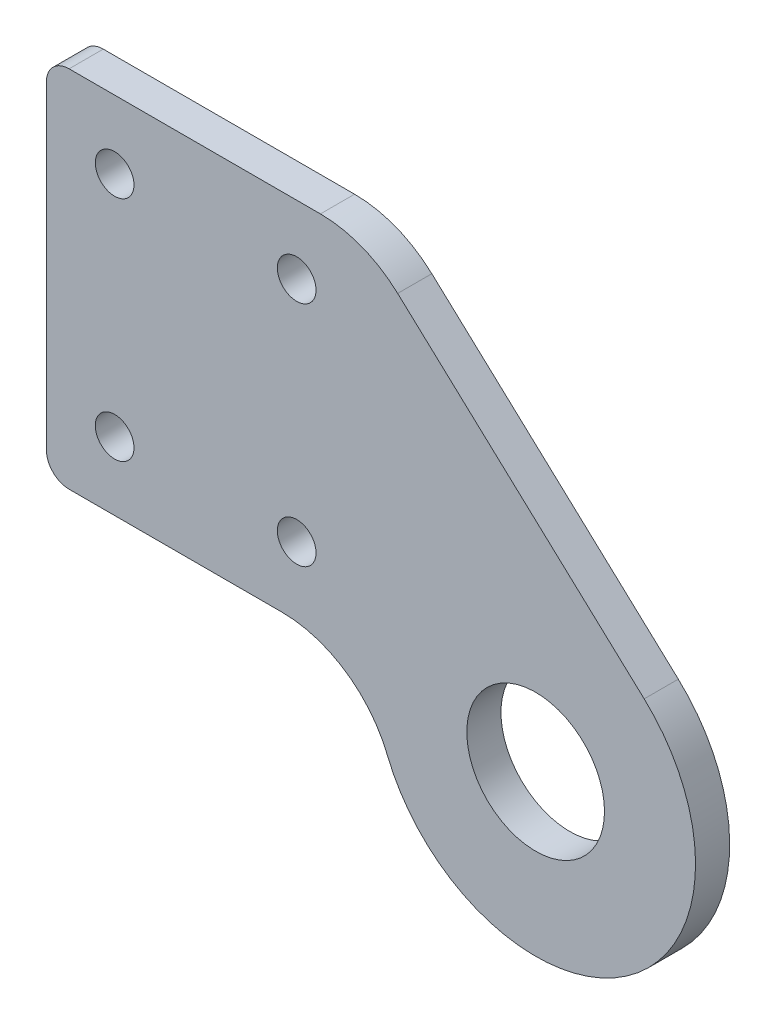
SolidWorks part; units mm, degrees
material "Hexcel AS4C (3000 Filaments)"
ref_plane "Plan de face" through (0, 0, 0) normal (0, 0, 1) x (1, 0, 0)
ref_plane "Plan de dessus" through (0, 0, 0) normal (0, 1, 0) x (1, 0, 0)
ref_plane "Plan de droite" through (0, 0, 0) normal (1, 0, 0) x (0, 0, -1)
sketch "Esquisse1" plane through (0, 0, 0) normal (0, 0, 1) x (1, 0, 0)
  line L0 (-7.5, 16.5) -> (4.7687, 5.1585)
  line L1 (-18.5, 13.5) -> (-10.5, 13.5) construction
  line L2 (-18.5, 13.5) -> (-18.5, 3.5) construction
  line L3 (-18.5, 3.5) -> (-10.5, 3.5) construction
  line L4 (-10.5, 13.5) -> (-10.5, 3.5) construction
  line L5 (-21.5, 16.5) -> (-7.5, 16.5)
  line L6 (-21.5, 16.5) -> (-21.5, 0.5)
  line L7 (-21.5, 0.5) -> (-7.5, 0.5)
  line L8 (-7.5, 16.5) -> (-7.5, 0.5) construction
  line L9 (-7.5, 0.5) -> (-7.5, 4.475) construction
  line L10 (-7.5, 4.475) -> (-5.4153, 4.475) construction
  line L11 (-7.5, 0.5) -> (-7.0072, 0.5)
  circle A0 centre (0, 0) radius 3.025
  circle A1 centre (0, 0) radius 7.025 construction
  circle A2 centre (-18.5, 13.5) radius 0.85
  circle A3 centre (-10.5, 13.5) radius 0.85
  circle A4 centre (-10.5, 3.5) radius 0.85
  circle A5 centre (-18.5, 3.5) radius 0.85
  arc A6 (-5.4153, 4.475) -> (4.7687, 5.1585) centre (0, 0) ccw construction
  arc A7 (-7.0072, 0.5) -> (4.7687, 5.1585) centre (0, 0) ccw
  dimension "D1" = 8
  dimension "D8" = 14.05
  dimension "D9" = 6.05
  dimension "D10" = 1.7
  dimension "D11" = 1.7
  dimension "D12" = 1.7
  dimension "D13" = 1.7
  dimension "D2" = 10
  dimension "D3" = 3
  dimension "D4" = 14
  dimension "D5" = 3
  dimension "D6" = 16
  dimension "D7" = 0.5
  dimension "D14" = 3.975
  dimension "D15" = 21.5
extrude "Boss.-Extru.1" add sketch "Esquisse1" along normal mid plane 1.5
fillet "Congé1" radius 5 2 edges at (-7.5, 16.5, 0) (-7.0072, 0.5, 0)
fillet "Congé2" radius 1 2 edges at (-21.5, 0.5, 0) (-21.5, 16.5, 0)
